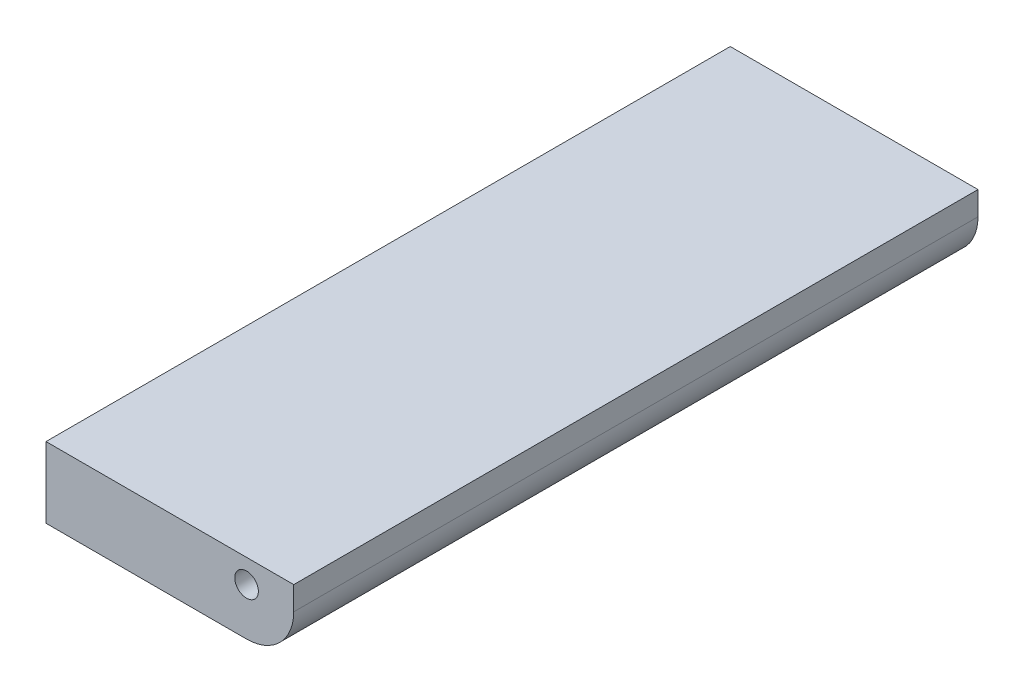
SolidWorks part; units mm, degrees
ref_plane "前视基准面" through (0, 0, 0) normal (0, 0, 1) x (1, 0, 0)
ref_plane "上视基准面" through (0, 0, 0) normal (0, 1, 0) x (1, 0, 0)
ref_plane "右视基准面" through (0, 0, 0) normal (1, 0, 0) x (0, 0, -1)
sketch "草图1" plane through (0, 0, 0) normal (0, 0, 1) x (1, 0, 0)
  line L1 (0, 0) -> (-105, 0)
  line L2 (0, 0) -> (0, -10)
  line L3 (-20, -30) -> (-105, -30)
  line L4 (-105, 0) -> (-105, -30)
  arc A0 (-20, -30) -> (0, -10) centre (-20, -10) ccw
  dimension "D1" = 20
  dimension "D2" = 105
  dimension "D3" = 30
extrude "凸台-拉伸1" add sketch "草图1" along normal blind 290
sketch "草图2" plane through (0, 0, 290) normal (0, 0, 1) x (1, 0, 0)
  circle A0 centre (-20, -10) radius 5
  dimension "D1" = 10
extrude "切除-拉伸1" cut sketch "草图2" against normal through all
